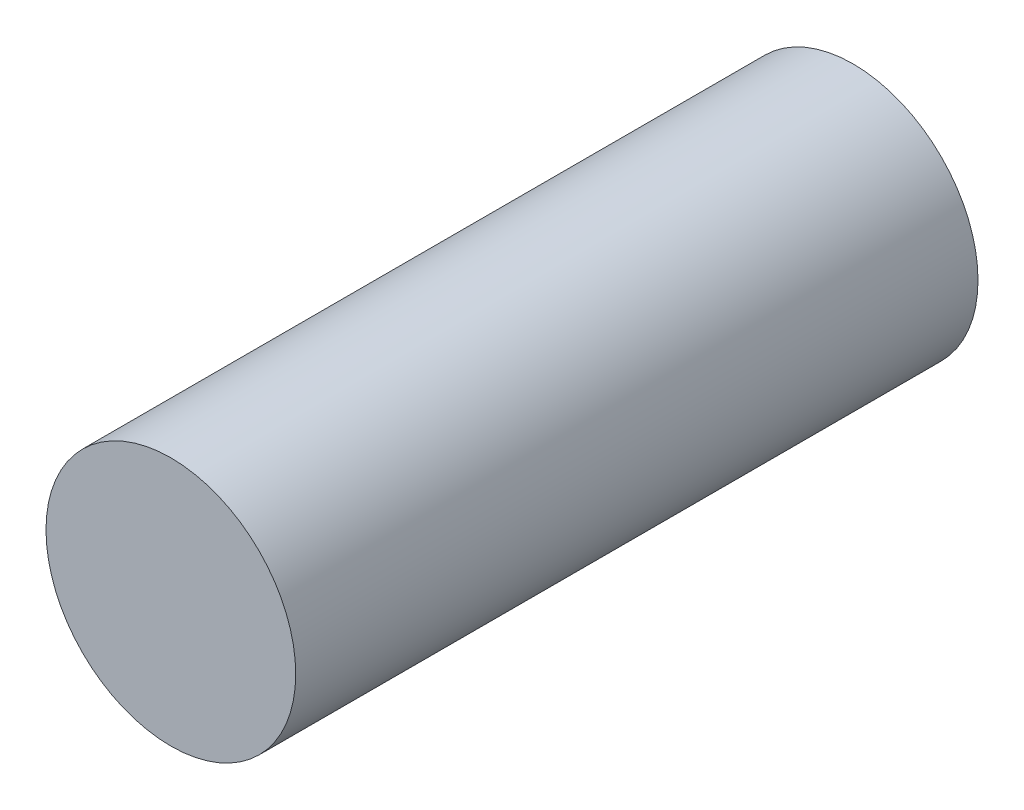
SolidWorks part; units mm, degrees
material "1023 Carbon Steel Sheet (SS)"
ref_plane "Front" through (0, 0, 0) normal (0, 0, 1) x (1, 0, 0)
ref_plane "Top" through (0, 0, 0) normal (0, 1, 0) x (1, 0, 0)
ref_plane "Right" through (0, 0, 0) normal (1, 0, 0) x (0, 0, -1)
sketch "Sketch1" plane through (0, 0, 0) normal (0, 0, 1) x (1, 0, 0)
  circle A0 centre (0, 0) radius 27.451
extrude "Boss-Extrude1" add sketch "Sketch1" along normal blind 150
